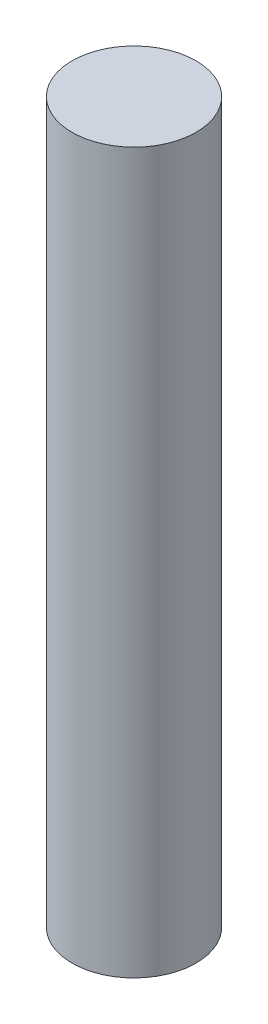
SolidWorks part; units mm, degrees
ref_plane "Front Plane" through (0, 0, 0) normal (0, 0, 1) x (1, 0, 0)
ref_plane "Top Plane" through (0, 0, 0) normal (0, 1, 0) x (1, 0, 0)
ref_plane "Right Plane" through (0, 0, 0) normal (1, 0, 0) x (0, 0, -1)
sketch "Sketch1" plane through (0, 0, 0) normal (0, 0, 1) x (1, 0, 0)
  line L0 (0, 0) -> (0, 39.1617)
  line L1 (0, 39.1617) -> (7, 39.1617)
  line L2 (7, 39.1617) -> (7, -42.0683)
  line L3 (7, -42.0683) -> (0, -42.0683)
  line L4 (0, -42.0683) -> (0, 0)
  dimension "D1" = 81.23
  dimension "D2" = 7
revolve "Revolve1" add sketch "Sketch1" angle 360 about L0
